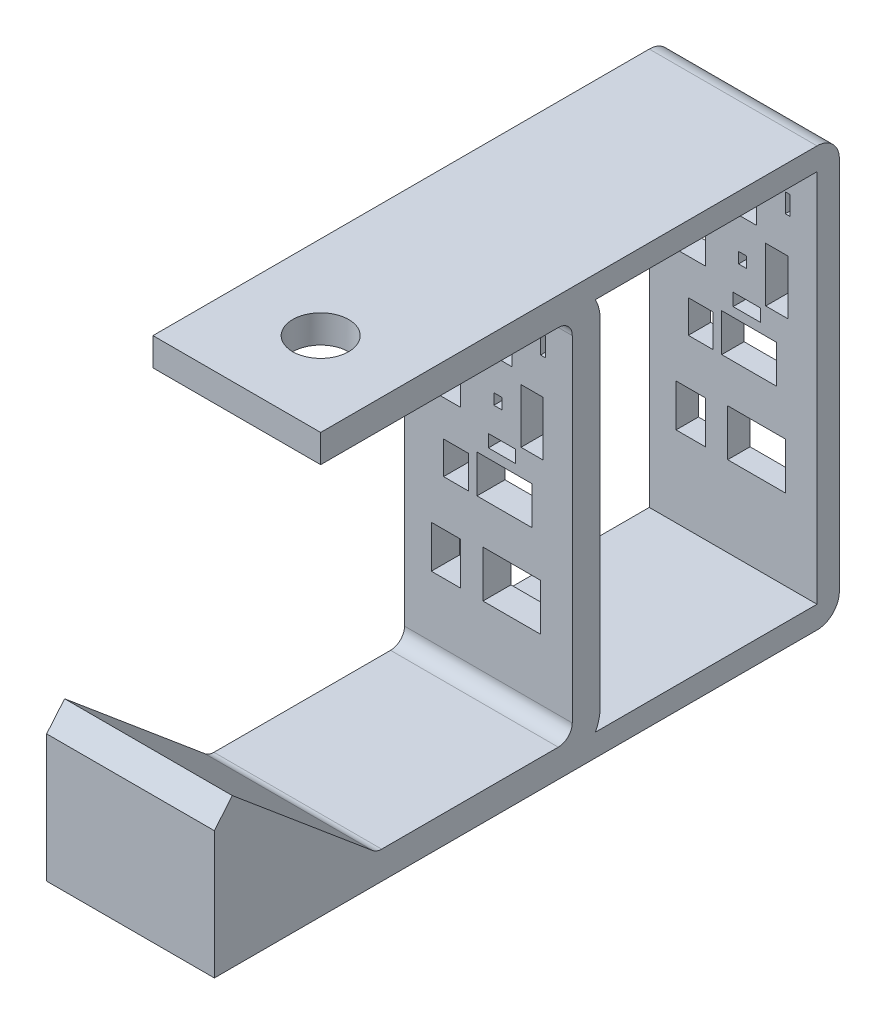
SolidWorks part; units mm, degrees
ref_plane "front" through (0, 0, 0) normal (0, 0, 1) x (1, 0, 0)
ref_plane "top" through (0, 0, 0) normal (0, 1, 0) x (1, 0, 0)
ref_plane "right" through (0, 0, 0) normal (1, 0, 0) x (0, 0, -1)
sketch "Sketch1" plane through (0, 0, 0) normal (1, 0, 0) x (0, 0, -1)
  line L0 (0, 0) -> (0, 82.55)
  line L1 (0, 82.55) -> (-57.15, 82.55)
  line L4 (-77.2165, 27.4943) -> (-44.45, 0)
  line L5 (-44.45, 0) -> (0, 0)
  dimension "D1" = 82.55
  dimension "D2" = 57.15
  dimension "D3" = 40
  dimension "D4" = 42.7736
  dimension "D5" = 44.45
extrude "Base-Extrude-Thin" add sketch "Sketch1" along normal mid plane 38.1 thin
sketch "Sketch2" plane through (0, 88.9, 0) normal (0, 1, 0) x (-1, 0, 0)
  line L0 (0, 50) -> (0, -50) construction
  line L1 (-19.05, 57.15) -> (19.05, 57.15) construction
  circle A0 centre (0, 38.1) radius 6.35
  dimension "D1" = 12.7
  dimension "D2" = 19.05
extrude "Cut-Extrude1" cut sketch "Sketch2" against normal up to next
sketch "Sketch3" plane through (0, 0, 0) normal (1, 0, 0) x (0, 0, -1)
  line L0 (-81.2982, 22.63) -> (-81.2982, -6.35)
  line L1 (-81.2982, -6.35) -> (-28.6776, -6.35)
  line L2 (-43.2944, -6.35) -> (-3.175, -6.35) construction
  line L3 (-81.2982, 22.63) -> (-49.4169, -4.1216) construction
  line L4 (-81.2982, 22.63) -> (-49.4169, -4.1216)
  arc A0 (-49.4169, -4.1216) -> (-43.2944, -6.35) centre (-43.2944, 3.175) ccw construction
  arc A1 (-49.4169, -4.1216) -> (-43.2944, -6.35) centre (-43.2944, 3.175) ccw
extrude "Boss-Extrude1" add sketch "Sketch3" along normal up to surface and the other way through all contours A1 L4 L0 L1
sketch "Sketch5" plane through (19.05, 0, 0) normal (1, 0, 0) x (0, 0, -1)
  line L0 (-3.175, 88.9) -> (60.6745, 88.9)
  line L1 (60.6745, 88.9) -> (60.6745, -6.35)
  line L2 (60.6745, -6.35) -> (-3.175, -6.35)
extrude "Extrude-Thin1" add sketch "Sketch5" against normal through all thin
sketch "Sketch4" plane through (0, 0, -6.35) normal (0, 0, -1) x (-1, 0, 0)
  line L1 (-11.8504, 76.2706) -> (-12.9613, 76.2706)
  line L2 (-11.8504, 76.2706) -> (-11.8504, 71.9502)
  line L3 (-11.8504, 71.9502) -> (-12.9613, 71.9502)
  line L4 (-12.9613, 76.2706) -> (-12.9613, 71.9502)
  line L5 (-1.2344, 59.2357) -> (-3.086, 59.2357)
  line L6 (-1.2344, 59.2357) -> (-1.2344, 56.7669)
  line L7 (-1.2344, 56.7669) -> (-3.086, 56.7669)
  line L8 (-3.086, 59.2357) -> (-3.086, 56.7669)
  line L9 (-9.8753, 45.6572) -> (2.5923, 45.6572)
  line L10 (-9.8753, 45.6572) -> (-9.8753, 37.0163)
  line L11 (-9.8753, 37.0163) -> (2.5923, 37.0163)
  line L12 (2.5923, 45.6572) -> (2.5923, 37.0163)
  line L13 (14.0723, 63.9265) -> (6.2955, 63.9265)
  line L14 (14.0723, 63.9265) -> (14.0723, 52.5699)
  line L15 (14.0723, 52.5699) -> (6.2955, 52.5699)
  line L16 (6.2955, 63.9265) -> (6.2955, 52.5699)
  line L17 (1.2344, 27.6347) -> (-11.8504, 27.6347)
  line L18 (1.2344, 27.6347) -> (1.2344, 17.0188)
  line L19 (1.2344, 17.0188) -> (-11.8504, 17.0188)
  line L20 (-11.8504, 27.6347) -> (-11.8504, 17.0188)
  line L21 (6.2955, 26.6472) -> (12.9613, 26.6472)
  line L22 (6.2955, 26.6472) -> (6.2955, 17.0188)
  line L23 (6.2955, 17.0188) -> (12.9613, 17.0188)
  line L24 (12.9613, 26.6472) -> (12.9613, 17.0188)
  line L25 (10.1839, 44.4228) -> (4.5673, 44.4228)
  line L26 (10.1839, 44.4228) -> (10.1839, 37.0163)
  line L27 (10.1839, 37.0163) -> (4.5673, 37.0163)
  line L28 (4.5673, 44.4228) -> (4.5673, 37.0163)
  line L29 (-5.308, 73.0611) -> (3.7032, 73.0611)
  line L30 (-5.308, 73.0611) -> (-5.308, 66.3953)
  line L31 (-5.308, 66.3953) -> (3.7032, 66.3953)
  line L32 (3.7032, 73.0611) -> (3.7032, 66.3953)
  line L33 (0, 50.5948) -> (-6.1721, 50.5948)
  line L34 (0, 50.5948) -> (0, 47.7557)
  line L35 (0, 47.7557) -> (-6.1721, 47.7557)
  line L36 (-6.1721, 50.5948) -> (-6.1721, 47.7557)
  line L37 (-12.4058, 63.9265) -> (-7.4065, 63.9265)
  line L38 (-12.4058, 63.9265) -> (-12.4058, 51.5823)
  line L39 (-12.4058, 51.5823) -> (-7.4065, 51.5823)
  line L40 (-7.4065, 63.9265) -> (-7.4065, 51.5823)
extrude "Cut-Extrude2" cut sketch "Sketch4" against normal up to next and the other way through all
fillet "Fillet1" radius 5.08 2 edges at (0, -6.35, -60.6745) (0, 88.9, -60.6745)
